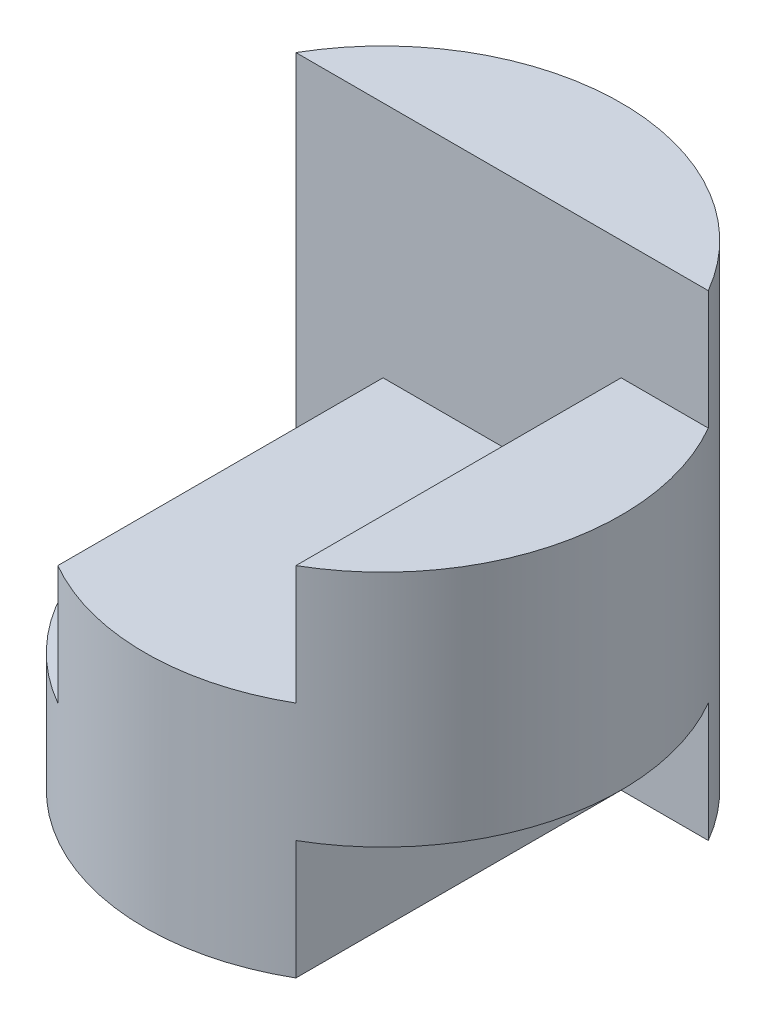
SolidWorks part; units mm, degrees
ref_plane "Front" through (0, 0, 0) normal (0, 0, 1) x (1, 0, 0)
ref_plane "Top" through (0, 0, 0) normal (0, 1, 0) x (1, 0, 0)
ref_plane "Right" through (0, 0, 0) normal (1, 0, 0) x (0, 0, -1)
sketch "Sketch1" plane through (0, 0, 0) normal (0, 1, 0) x (1, 0, 0)
  circle A0 centre (0, 0) radius 2
  dimension "D1" = 4
extrude "Boss-Extrude1" add sketch "Sketch1" along normal blind 4
sketch "Sketch2" plane through (0, 0, 0) normal (0, 0, 1) x (1, 0, 0)
  line L0 (-2, 4) -> (1, 4)
  line L2 (2, 0) -> (2, 4) construction
  line L3 (2, 1) -> (1, 1)
  line L5 (1, 2) -> (-1, 2)
  line L8 (-2, 3) -> (-2, 4)
  line L9 (-2, 1) -> (-1, 1)
  line L14 (1, 1) -> (2, 1)
  line L15 (1, 1) -> (1, 0)
  line L16 (1, 0) -> (2, 0)
  line L17 (2, 1) -> (2, 0)
  line L18 (-2, 4) -> (-2, 0) construction
  line L19 (-1, 1) -> (-1, 2)
  line L20 (-2, 3) -> (-2, 1)
  line L21 (1, 2) -> (1, 3)
  line L23 (1, 3) -> (2, 3)
  line L24 (2, 3) -> (2, 4)
  line L25 (2, 4) -> (1, 4)
  dimension "D1" = 1
  dimension "D3" = 1
extrude "Cut-Extrude1" cut sketch "Sketch2" against normal blind 1 and the other way blind 3
